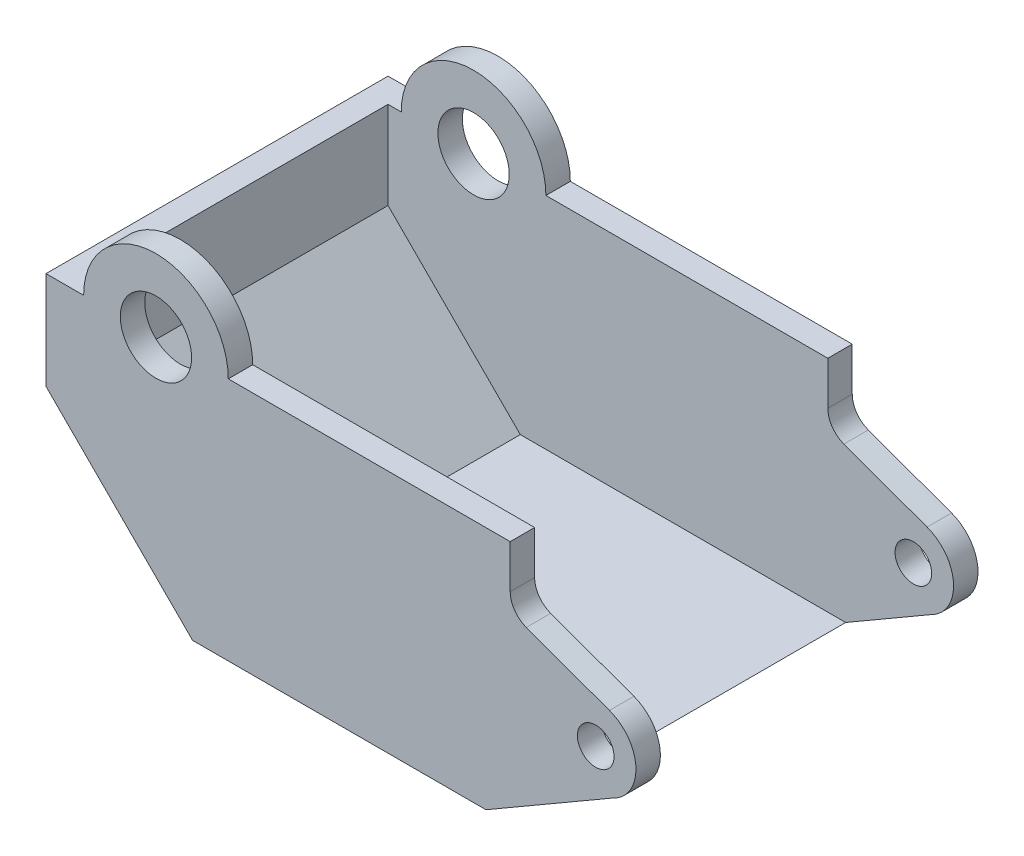
SolidWorks part; units mm, degrees
material "AISI 1035 Steel (SS)"
ref_plane "Front Plane" through (0, 0, 0) normal (0, 0, 1) x (1, 0, 0)
ref_plane "Top Plane" through (0, 0, 0) normal (0, 1, 0) x (1, 0, 0)
ref_plane "Right Plane" through (0, 0, 0) normal (1, 0, 0) x (0, 0, -1)
sketch "Sketch1" plane through (0, 0, 0) normal (0, 0, 1) x (1, 0, 0)
  line L0 (-17.8698, 7.8816) -> (-20.3539, 7.8816)
  line L1 (-20.3539, 7.8816) -> (-20.3539, 1.43)
  line L2 (-20.3539, 1.43) -> (-10.6765, -8.25)
  line L3 (-10.6765, -8.25) -> (8.6933, -8.25)
  line L4 (17.047, -3.4059) -> (8.6933, -8.25)
  line L5 (-8.3194, 7.8816) -> (10.2937, 7.8816)
  line L6 (10.2937, 7.8816) -> (10.2937, 5.0215)
  line L7 (11.3549, 3.5059) -> (16.8489, 1.5059)
  arc A1 (-8.3194, 7.8816) -> (-17.8698, 7.8816) centre (-13.0946, 7.8816) ccw
  arc A3 (17.047, -3.4059) -> (16.8489, 1.5059) centre (15.9401, -0.9906) ccw
  arc A4 (10.2937, 5.0215) -> (11.3549, 3.5059) centre (11.9066, 5.0215) ccw
  dimension "D1" = 1.6129
  dimension "D2" = 9.5504
  dimension "D4" = 5.3137
  dimension "D6" = 7.2593
  dimension "D7" = 23.3883
  dimension "D9" = 6.0122
  dimension "D13" = 19.3698
  dimension "D14" = 6.4516
  dimension "D8" = 5.6464
  dimension "D10" = 16.1315
  dimension "D11" = 2.86
  dimension "D12" = 9.6774
extrude "Boss-Extrude2" add sketch "Sketch1" along normal blind 22.5831
shell "Shell3" thickness 1.6129
sketch "Sketch2" plane through (0, 0, 22.5831) normal (0, 0, 1) x (1, 0, 0)
  circle A0 centre (-13.0946, 7.8816) radius 2.3546
  circle A1 centre (15.9401, -0.9906) radius 1.209
extrude "Cut-Extrude1" cut sketch "Sketch2" against normal through all
